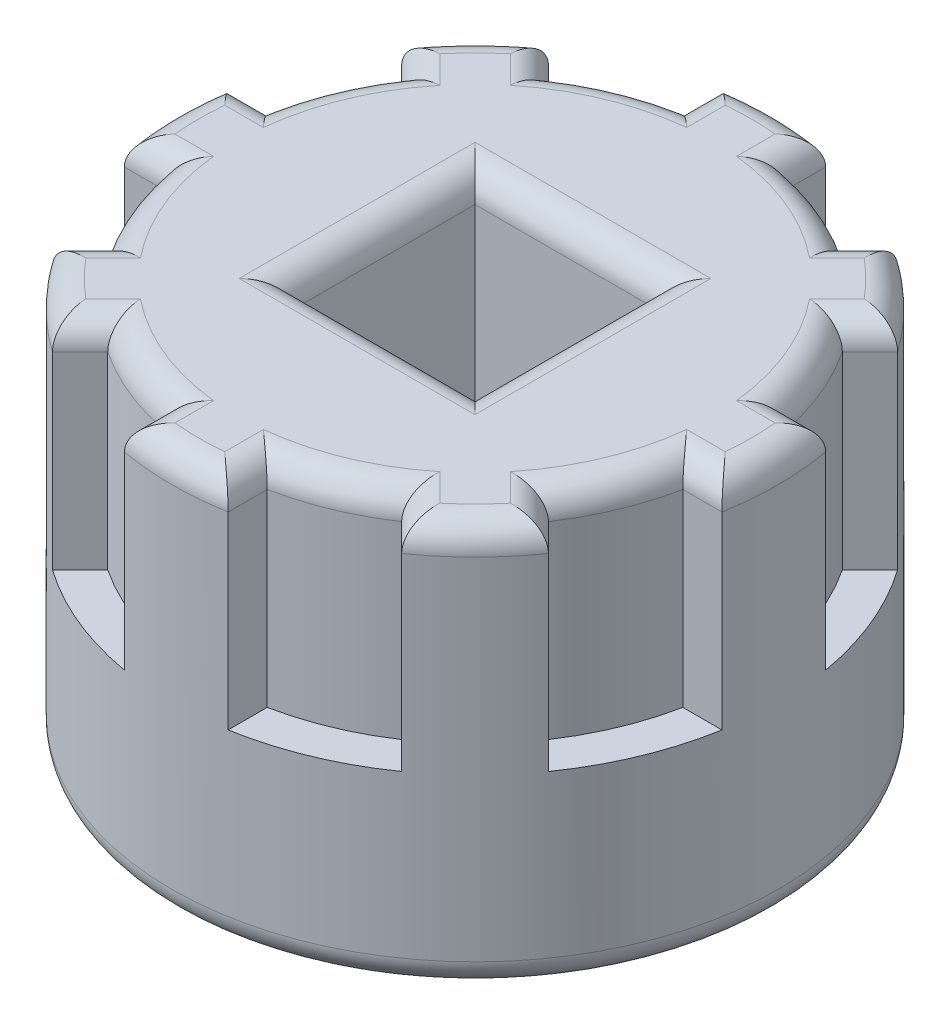
SolidWorks part; units mm, degrees
ref_plane "Front Plane" through (0, 0, 0) normal (0, 0, 1) x (1, 0, 0)
ref_plane "Top Plane" through (0, 0, 0) normal (0, 1, 0) x (1, 0, 0)
ref_plane "Right Plane" through (0, 0, 0) normal (1, 0, 0) x (0, 0, -1)
sketch "Sketch1" plane through (0, 0, 0) normal (0, 1, 0) x (1, 0, 0)
  circle A0 centre (0, 0) radius 5.715
  dimension "D1" = 11.43
extrude "Boss-Extrude2" add sketch "Sketch1" along normal blind 3.556
sketch "Sketch2" plane through (0, 3.556, 0) normal (0, 1, 0) x (1, 0, 0)
  line L0 (-0.9779, 5.6307) -> (-0.9779, 4.8941)
  line L1 (0.9779, 5.6307) -> (0.9779, 4.8941)
  line L2 (3.29, 4.673) -> (2.7692, 4.1521)
  line L3 (4.673, 3.29) -> (4.1521, 2.7692)
  line L4 (5.6307, 0.9779) -> (4.8941, 0.9779)
  line L5 (5.6307, -0.9779) -> (4.8941, -0.9779)
  line L6 (4.673, -3.29) -> (4.1521, -2.7692)
  line L7 (3.29, -4.673) -> (2.7692, -4.1521)
  line L8 (0.9779, -5.6307) -> (0.9779, -4.8941)
  line L9 (-0.9779, -5.6307) -> (-0.9779, -4.8941)
  line L10 (-3.29, -4.673) -> (-2.7692, -4.1521)
  line L11 (-4.673, -3.29) -> (-4.1521, -2.7692)
  line L12 (-5.6307, -0.9779) -> (-4.8941, -0.9779)
  line L13 (-5.6307, 0.9779) -> (-4.8941, 0.9779)
  line L14 (-4.673, 3.29) -> (-4.1521, 2.7692)
  line L15 (-3.29, 4.673) -> (-2.7692, 4.1521)
  circle A0 centre (0, 0) radius 5.715
  circle A1 centre (0, 0) radius 4.9909
  point P37 (0, 0)
  circle M4 centre (0, 0) radius 5.715
  dimension "D2" = 11.43
  dimension "D1" = 0.9779
  dimension "D3" = 0.9779
  dimension "D4" = 0.7366
  dimension "D5" = 0.7366
  dimension "D6" = 8
extrude "Boss-Extrude3" add sketch "Sketch2" along normal blind 4.064 contours A1 | A1 L1 L0 M4 | A1 L15 L14 M4 | A1 L13 L12 M4 | A1 L11 L10 M4 | A1 L9 L8 M4 | A1 L7 L6 M4 | A1 L5 L4 M4 | A1 L3 L2 M4
sketch "Sketch3" plane through (0, 7.62, 0) normal (0, 1, 0) x (1, 0, 0)
  line L1 (-1.7145, -1.7145) -> (1.7145, -1.7145)
  line L2 (-1.7145, -1.7145) -> (-1.7145, 1.7145)
  line L3 (-1.7145, 1.7145) -> (1.7145, 1.7145)
  line L4 (1.7145, -1.7145) -> (1.7145, 1.7145)
  line L5 (-1.7145, -1.7145) -> (1.7145, 1.7145) construction
  line L6 (-1.7145, 1.7145) -> (1.7145, -1.7145) construction
  point P0 (0, 0)
  dimension "D1" = 3.429
  dimension "D2" = 3.429
extrude "Cut-Extrude1" cut sketch "Sketch3" against normal through all both and the other way through all
fillet "Fillet1" radius 0.508 41 edges at (0, 0, 5.715) (-1.7145, 0, 0) (0, 0, -1.7145) (1.7145, 0, 0) (0, 0, 1.7145) (0, 7.62, 5.715) (-0.9779, 7.62, 5.2624) (-1.9099, 7.62, 4.6109) (-3.0296, 7.62, 4.4126) (-4.0411, 7.62, 4.0411) (-4.4126, 7.62, 3.0296) (-4.6109, 7.62, 1.9099) (-5.2624, 7.62, 0.9779) (-5.715, 7.62, 0) (-5.2624, 7.62, -0.9779) (-4.6109, 7.62, -1.9099) (-4.4126, 7.62, -3.0296) (-4.0411, 7.62, -4.0411) (-3.0296, 7.62, -4.4126) (-1.9099, 7.62, -4.6109) (-0.9779, 7.62, -5.2624) (0, 7.62, -5.715) (0.9779, 7.62, -5.2624) (1.9099, 7.62, -4.6109) (3.0296, 7.62, -4.4126) (4.0411, 7.62, -4.0411) (4.4126, 7.62, -3.0296) (4.6109, 7.62, -1.9099) (5.2624, 7.62, -0.9779) (5.715, 7.62, 0) (5.2624, 7.62, 0.9779) (4.6109, 7.62, 1.9099) (4.4126, 7.62, 3.0296) (4.0411, 7.62, 4.0411) (3.0296, 7.62, 4.4126) (1.9099, 7.62, 4.6109) (0.9779, 7.62, 5.2624) (0, 7.62, -1.7145) (-1.7145, 7.62, 0) (0, 7.62, 1.7145) (1.7145, 7.62, 0)
